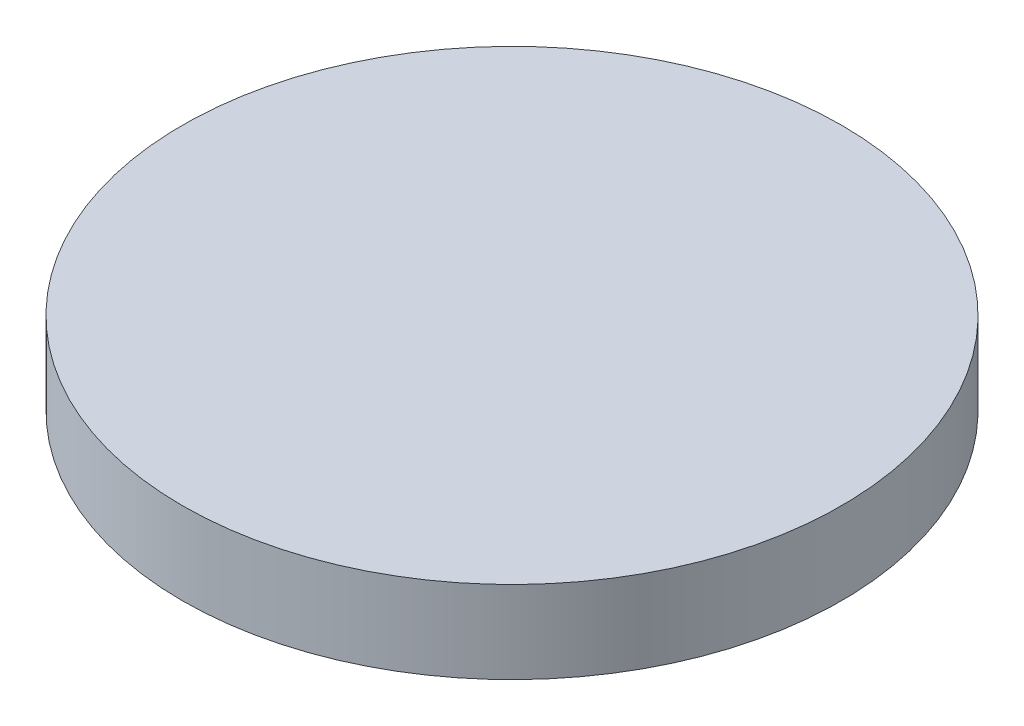
SolidWorks part; units mm, degrees
ref_plane "Front Plane" through (0, 0, 0) normal (0, 0, 1) x (1, 0, 0)
ref_plane "Top Plane" through (0, 0, 0) normal (0, 1, 0) x (1, 0, 0)
ref_plane "Right Plane" through (0, 0, 0) normal (1, 0, 0) x (0, 0, -1)
sketch "Sketch1" plane through (0, 0, 0) normal (0, 1, 0) x (1, 0, 0)
  circle A0 centre (0, 0) radius 40
  dimension "D1" = 80
extrude "Boss-Extrude1" add sketch "Sketch1" along normal blind 10
